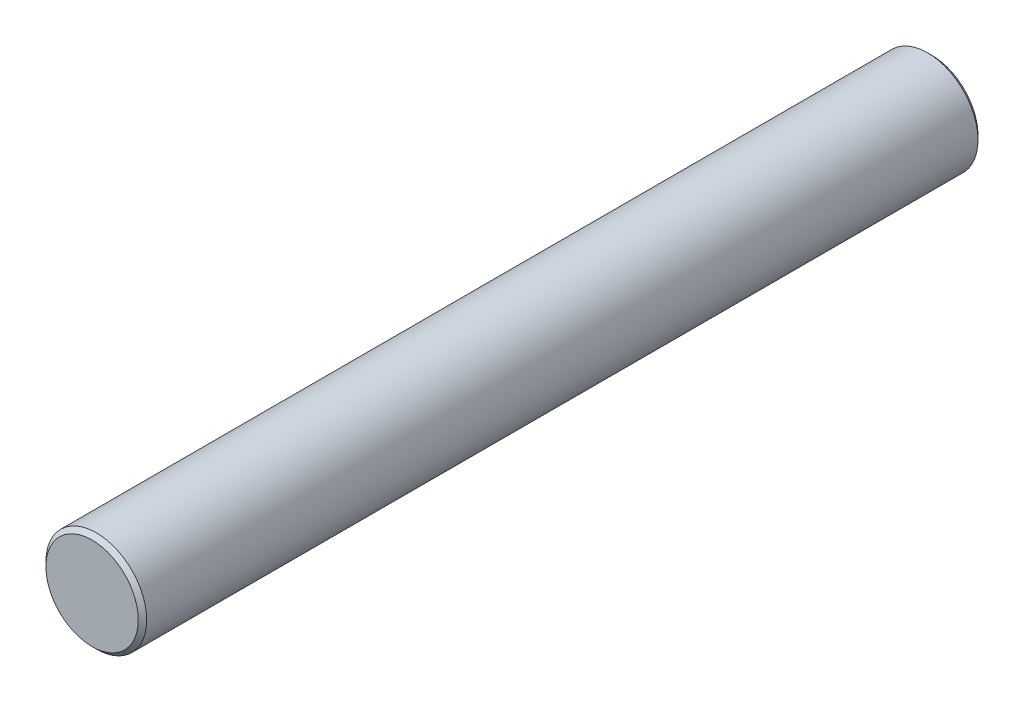
SolidWorks part; units mm, degrees
ref_plane "Plan de face" through (0, 0, 0) normal (0, 0, 1) x (1, 0, 0)
ref_plane "Plan de dessus" through (0, 0, 0) normal (0, 1, 0) x (1, 0, 0)
ref_plane "Plan de droite" through (0, 0, 0) normal (1, 0, 0) x (0, 0, -1)
sketch "Esquisse1" plane through (0, 0, 0) normal (0, 0, 1) x (1, 0, 0)
  circle A0 centre (0, 0) radius 6
  dimension "D1" = 12
extrude "Boss.-Extru.1" add sketch "Esquisse1" along normal blind 100
chamfer "Chanfrein1" distance 0.5 angle 45 2 edges at (6, 0, 0) (6, 0, 100)
